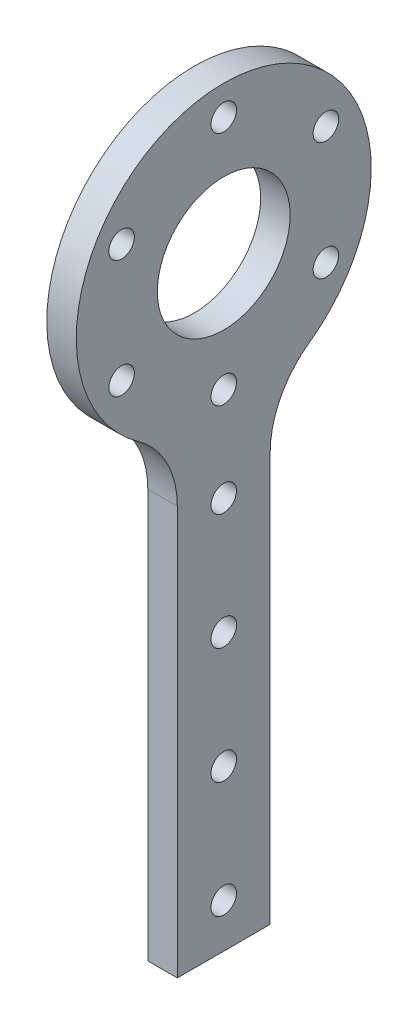
SolidWorks part; units mm, degrees
ref_plane "Front Plane" through (0, 0, 0) normal (0, 0, 1) x (1, 0, 0)
ref_plane "Top Plane" through (0, 0, 0) normal (0, 1, 0) x (1, 0, 0)
ref_plane "Right Plane" through (0, 0, 0) normal (1, 0, 0) x (0, 0, -1)
sketch "Sketch1" plane through (0, 0, 0) normal (1, 0, 0) x (0, 0, -1)
  line L0 (-10, -30.1341) -> (10, -30.1341) construction
  line L1 (-10, -30.1341) -> (-10, -130.1341)
  line L2 (-10, -130.1341) -> (10, -130.1341)
  line L3 (10, -130.1341) -> (10, -30.1341)
  arc A1 (10, -30.1341) -> (-10, -30.1341) centre (0, 0) ccw
  point P7 (0, -30.1341)
  dimension "D1" = 31.75
  dimension "D3" = 100
extrude "Boss-Extrude1" add sketch "Sketch1" along normal blind 6.35 contours A1 L0 | L0 L1 L2 L3
fillet "Fillet1" radius 20 2 edges at (3.175, -30.1341, -10) (3.175, -30.1341, 10)
sketch "Sketch2" plane through (6.35, 0, 0) normal (1, 0, 0) x (0, 0, -1)
  circle A0 centre (0, 0) radius 14.3
  circle A1 centre (0, 25.4) radius 2.75
  circle A2 centre (21.997, 12.7) radius 2.75
  circle A3 centre (21.997, -12.7) radius 2.75
  circle A4 centre (0, -25.4) radius 2.75
  circle A5 centre (-21.997, -12.7) radius 2.75
  circle A6 centre (-21.997, 12.7) radius 2.75
  point P18 (0, 0)
  dimension "D1" = 28.6
  dimension "D2" = 5.5
  dimension "D3" = 25.4
  dimension "D4" = 6
extrude "Cut-Extrude1" cut sketch "Sketch2" against normal through all
sketch "Sketch3" plane through (6.35, 0, 0) normal (1, 0, 0) x (0, 0, -1)
  circle A0 centre (0, -120.6366) radius 2.75
  circle A1 centre (0, -95.6366) radius 2.75
  circle A2 centre (0, -70.6366) radius 2.75
  circle A3 centre (0, -45.6366) radius 2.75
  dimension "D1" = 5.5
  dimension "D2" = 5.5
  dimension "D3" = 5.5
  dimension "D4" = 5.5
  dimension "D5" = 25
  dimension "D6" = 25
  dimension "D7" = 25
extrude "Cut-Extrude2" cut sketch "Sketch3" against normal through all
